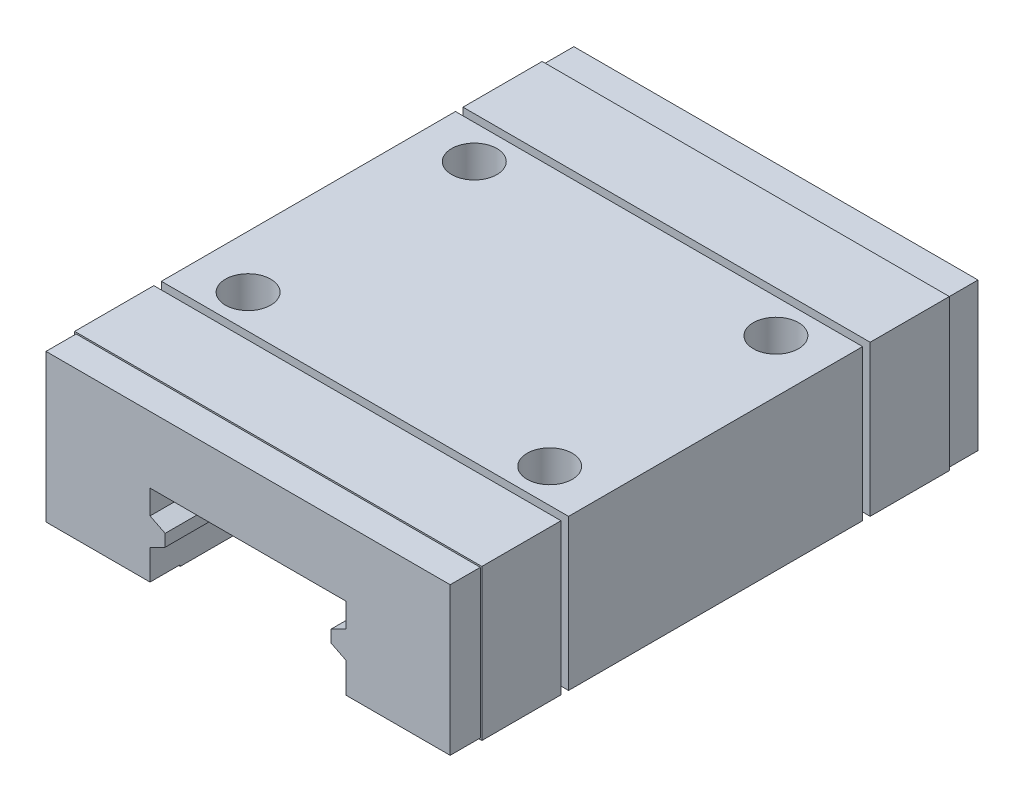
SolidWorks part; units mm, degrees
ref_plane "前视基准面" through (0, 0, 0) normal (0, 0, 1) x (1, 0, 0)
ref_plane "上视基准面" through (0, 0, 0) normal (0, 1, 0) x (1, 0, 0)
ref_plane "右视基准面" through (0, 0, 0) normal (1, 0, 0) x (0, 0, -1)
sketch "草图2" plane through (0, 0, 0) normal (0, 0, 1) x (1, 0, 0)
  line L1 (-13.5, -5) -> (13.5, -5)
  line L2 (-13.5, -5) -> (-13.5, 5)
  line L3 (-13.5, 5) -> (13.5, 5)
  line L4 (13.5, -5) -> (13.5, 5)
  line L5 (-13.5, -5) -> (13.5, 5) construction
  line L6 (-13.5, 5) -> (13.5, -5) construction
  point P0 (0, 0)
  dimension "D1" = 10
  dimension "D2" = 27
extrude "凸台-拉伸1" add sketch "草图2" along normal mid plane 35
sketch "草图3" plane through (0, 0, 17.5) normal (0, 0, 1) x (1, 0, 0)
  line L0 (0, 0) -> (0, 5) construction
  line L1 (13.5, 5) -> (-13.5, 5) construction
  line L3 (2.3094, 2.5) -> (1.1547, 4.5)
  line L4 (1.1547, 4.5) -> (-1.1547, 4.5)
  line L5 (-1.1547, 4.5) -> (-2.3094, 2.5)
  line L6 (-2.3094, 2.5) -> (-1.1547, 0.5)
  line L7 (-1.1547, 0.5) -> (1.1547, 0.5)
  line L8 (1.1547, 0.5) -> (2.3094, 2.5)
  circle A0 centre (0, 2.5) radius 2 construction
  dimension "D1" = 4
  dimension "D2" = 0.5
extrude "凸台-拉伸2" [suppressed] add sketch "草图3" along normal blind 4.5
sketch "草图4" plane through (0, 5, 0) normal (0, 1, 0) x (1, 0, 0)
  line L1 (-10, -7.5) -> (10, -7.5) construction
  line L2 (-10, -7.5) -> (-10, 7.5) construction
  line L3 (-10, 7.5) -> (10, 7.5) construction
  line L4 (10, -7.5) -> (10, 7.5) construction
  line L5 (-10, -7.5) -> (10, 7.5) construction
  line L6 (-10, 7.5) -> (10, -7.5) construction
  circle A0 centre (-10, 7.5) radius 1.5
  circle A1 centre (10, 7.5) radius 1.5
  circle A2 centre (-10, -7.5) radius 1.5
  circle A3 centre (10, -7.5) radius 1.5
  point P0 (0, 0)
  dimension "D3" = 3
  dimension "D1" = 15
  dimension "D2" = 20
extrude "切除-拉伸1" cut sketch "草图4" against normal blind 4
sketch "草图5" plane through (0, 0, 17.5) normal (0, 0, 1) x (1, 0, 0)
  line L0 (0, 0) -> (0, -7.6689) construction
  line L1 (-13.5, -5) -> (13.5, -5) construction
  line L2 (-6.5, -9.0812) -> (6.5, -9.0812)
  line L3 (-6.5, -9.0812) -> (-6.5, 0.5)
  line L4 (-6.5, 0.5) -> (6.5, 0.5)
  line L5 (6.5, -9.0812) -> (6.5, 0.5)
  line L6 (-6.5, -9.0812) -> (6.5, 0.5) construction
  line L7 (-6.5, 0.5) -> (6.5, -9.0812) construction
  point P3 (0, -4.2906)
  dimension "D1" = 13
  dimension "D2" = 5.5
sketch "草图6" plane through (0, 5, 0) normal (0, 1, 0) x (1, 0, 0)
  line L0 (0, -17.5) -> (0, 17.5) construction
  line L1 (13.5, -17.5) -> (-13.5, -17.5) construction
  line L2 (13.5, 17.5) -> (-13.5, 17.5) construction
  line L3 (-13.5, -17.5) -> (-13.5, 17.5) construction
  line L10 (-13.5, 0) -> (13.5, 0) construction
  line L11 (13.5, 9.75) -> (-13.5, 9.75)
  line L12 (13.5, 9.75) -> (13.5, 10.25)
  line L13 (13.5, 10.25) -> (-13.5, 10.25)
  line L14 (-13.5, 9.75) -> (-13.5, 10.25)
  line L15 (13.5, 9.75) -> (-13.5, 10.25) construction
  line L16 (13.5, 10.25) -> (-13.5, 9.75) construction
  line L17 (13.5, -17.5) -> (13.5, 17.5) construction
  point P13 (0, 10)
  dimension "D2" = 0.5
  dimension "D4" = 10
extrude "切除-拉伸2" cut sketch "草图6" against normal blind 0.5
sketch "草图7" plane through (-13.5, 0, 0) normal (-1, 0, 0) x (0, 0, 1)
  line L0 (-10.25, 4.5) -> (-10.25, 5) construction
  line L1 (-9.75, 4.5) -> (-10.25, 4.5)
  line L2 (-9.75, 4.5) -> (-9.75, -5)
  line L3 (-9.75, -5) -> (-10.25, -5)
  line L4 (-10.25, 4.5) -> (-10.25, -5)
  line L5 (17.5, -5) -> (-17.5, -5) construction
extrude "切除-拉伸3" cut sketch "草图7" against normal blind 0.5
sketch "草图12" plane through (0, 0, -17.5) normal (0, 0, -1) x (-1, 0, 0)
  line L4 (-13.5, 5) -> (13.5, 5) construction
  line L5 (-13.5, -5) -> (-13.5, 5) construction
  line L6 (13.5, -5) -> (-13.5, -5) construction
  line L7 (13.5, 5) -> (13.5, -5) construction
  line L8 (-13.4, 4.9) -> (-13.4, -4.9)
  line L9 (-13.4, -4.9) -> (13.4, -4.9)
  line L10 (13.4, -4.9) -> (13.4, 4.9)
  line L11 (13.4, 4.9) -> (-13.4, 4.9)
  line L12 (-13.4, 4.9) -> (-13.4, -4.9)
  line L13 (-13.4, -4.9) -> (13.4, -4.9)
  line L14 (13.4, -4.9) -> (13.4, 4.9)
  line L15 (13.4, 4.9) -> (-13.4, 4.9)
  line L16 (-13.5, 5) -> (13.5, 5)
  line L17 (-13.5, -5) -> (-13.5, 5)
  line L18 (13.5, -5) -> (-13.5, -5)
  line L19 (13.5, 5) -> (13.5, -5)
  dimension "D1" = 0.1
extrude "切除-拉伸5" cut sketch "草图12" against normal blind 2
mirror "镜向1" about plane through (0, 0, 0) normal (0, 1, 0) of "切除-拉伸2"
mirror "镜向2" about plane through (0, 0, 0) normal (1, 0, 0) of "切除-拉伸3"
mirror "镜向3" about plane through (0, 0, 0) normal (0, 0, 1) of "切除-拉伸5", "镜向2", "镜向1", "切除-拉伸2", "切除-拉伸3"
extrude "切除-拉伸4" cut sketch "草图5" against normal blind 97
sketch "草图9" plane through (0, 0, 17.5) normal (0, 0, 1) x (1, 0, 0)
  line L0 (-9.4656, -2) -> (9.6798, -2) construction
  line L1 (6.5, 0.5) -> (-6.5, 0.5) construction
  line L2 (-6.5, -1.1) -> (-5.5, -1.6)
  line L3 (-6.5, 0.5) -> (-6.5, -4.9) construction
  line L4 (-5.5, -1.6) -> (-5.5, -2.4)
  line L5 (-5.5, -2.4) -> (-6.5, -2.9)
  line L6 (-6.5, -2.9) -> (-6.5, -1.1)
  line L7 (0, 0.5) -> (0, -5.8047) construction
  line L8 (5.5, -1.6) -> (5.5, -2.4)
  line L9 (6.5, -1.1) -> (5.5, -1.6)
  line L10 (6.5, -2.9) -> (6.5, -1.1)
  line L11 (5.5, -2.4) -> (6.5, -2.9)
  dimension "D1" = 2.5
  dimension "D2" = 0.8
  dimension "D3" = 1
  dimension "D4" = 1.8
  dimension "D5" = 0.4
extrude "凸台-拉伸3" add sketch "草图9" against normal up to surface (35 mm away) up to face at (0, -1.1, -17.5)
